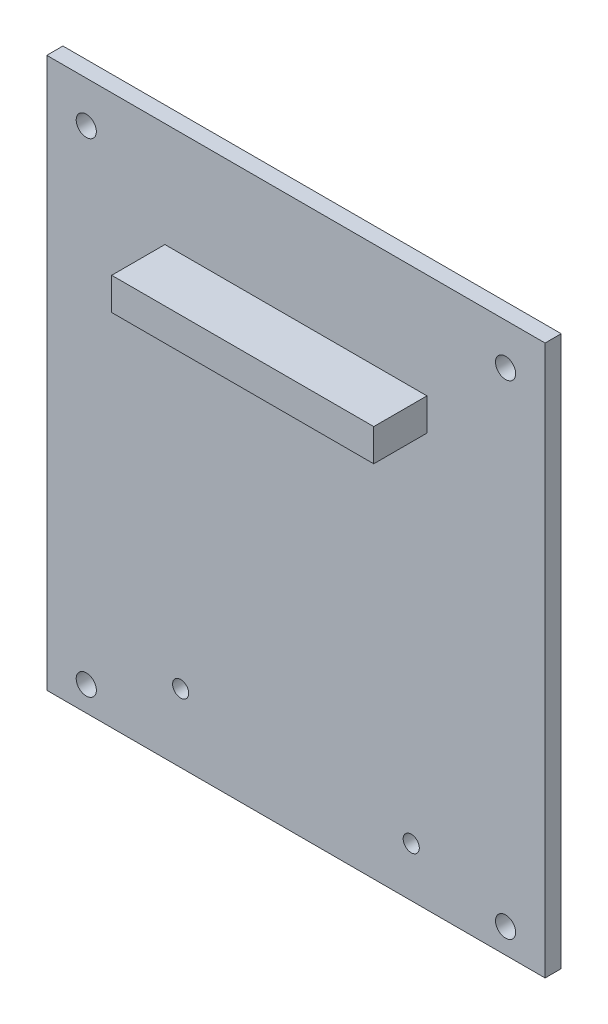
SolidWorks part; units mm, degrees
ref_plane "Front Plane" through (0, 0, 0) normal (0, 0, 1) x (1, 0, 0)
ref_plane "Top Plane" through (0, 0, 0) normal (0, 1, 0) x (1, 0, 0)
ref_plane "Right Plane" through (0, 0, 0) normal (1, 0, 0) x (0, 0, -1)
sketch "Sketch1" plane through (0, 0, 0) normal (0, 0, 1) x (1, 0, 0)
  line L0 (6.223, 80.1116) -> (72.263, 80.1116) construction
  line L1 (0, 86.614) -> (78.486, 86.614)
  line L2 (0, 86.614) -> (0, 0)
  line L3 (0, 0) -> (78.486, 0)
  line L4 (78.486, 86.614) -> (78.486, 0)
  line L5 (72.263, 80.1116) -> (72.263, 3.9116) construction
  line L6 (72.263, 3.9116) -> (6.223, 3.9116) construction
  line L7 (6.223, 3.9116) -> (6.223, 80.1116) construction
  line L8 (39.243, 86.614) -> (39.243, 0) construction
  line L9 (6.223, 42.0116) -> (72.263, 42.0116) construction
  circle A0 centre (6.223, 80.1116) radius 1.5875
  circle A1 centre (72.263, 80.1116) radius 1.5875
  circle A2 centre (72.263, 3.9116) radius 1.5875
  circle A3 centre (6.223, 3.9116) radius 1.5875
  point P18 (39.243, 42.0116)
  point P22 (39.243, 43.307)
  dimension "D3" = 3.175
  dimension "D1" = 76.2
  dimension "D2" = 66.04
  dimension "D4" = 78.486
  dimension "D5" = 86.614
  dimension "D6" = 2.5908
extrude "Boss-Extrude1" add sketch "Sketch1" along normal blind 2.54
sketch "Sketch2" plane through (0, 0, 2.54) normal (0, 0, 1) x (1, 0, 0)
  line L0 (39.243, 86.614) -> (39.243, 70.104) construction
  line L1 (18.6055, 70.104) -> (59.8805, 70.104)
  line L2 (18.6055, 70.104) -> (18.6055, 65.024)
  line L3 (18.6055, 65.024) -> (59.8805, 65.024)
  line L4 (59.8805, 70.104) -> (59.8805, 65.024)
  line L5 (78.486, 86.614) -> (0, 86.614) construction
  dimension "D1" = 5.08
  dimension "D2" = 41.275
  dimension "D3" = 16.51
extrude "Boss-Extrude2" add sketch "Sketch2" along normal blind 8.382
sketch "Sketch3" plane through (0, 0, 2.54) normal (0, 0, 1) x (1, 0, 0)
  line L0 (57.404, 7.8105) -> (57.404, 3.9116) construction
  line L1 (57.404, 3.9116) -> (72.263, 3.9116) construction
  line L2 (0, 0) -> (78.486, 0) construction
  circle A0 centre (72.263, 3.9116) radius 1.5875 construction
  dimension "D1" = 14.859
  dimension "D2" = 3.8989
sketch "Sketch4" plane through (0, 0, 2.54) normal (0, 0, 1) x (1, 0, 0)
  line L0 (0, 0) -> (78.486, 0) construction
  line L6 (21.082, 10.7569) -> (57.404, 10.7569) construction
  line L7 (39.243, 10.7569) -> (39.243, 0) construction
  line L9 (57.404, 10.7569) -> (57.404, 7.8105) construction
  circle A0 centre (21.082, 10.7569) radius 1.27
  circle A2 centre (57.404, 7.8105) radius 1.27
  dimension "D6" = 2.54
  dimension "D4" = 10.7569
  dimension "D5" = 36.322
  dimension "D7" = 2.9464
extrude "Cut-Extrude1" cut sketch "Sketch4" against normal up to surface (2.54 mm away) up to face at (39.243, 43.307, 0)
